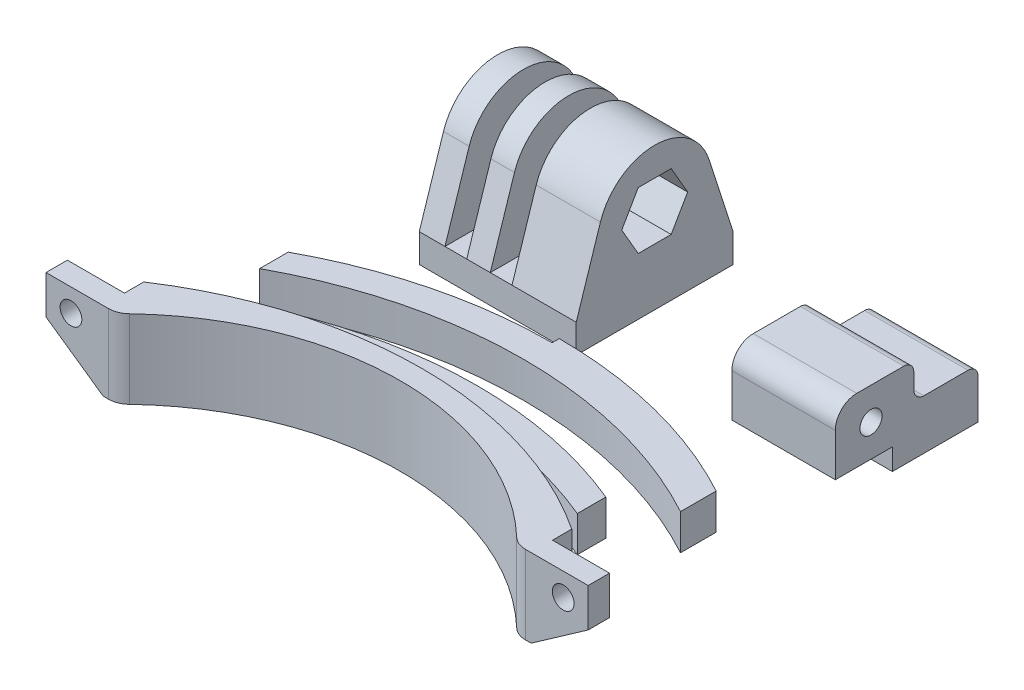
SolidWorks part; units mm, degrees
ref_plane "Front Plane" through (0, 0, 0) normal (0, 0, 1) x (1, 0, 0)
ref_plane "Top Plane" through (0, 0, 0) normal (0, 1, 0) x (1, 0, 0)
ref_plane "Right Plane" through (0, 0, 0) normal (1, 0, 0) x (0, 0, -1)
sketch "Sketch1" plane through (0, 0, 0) normal (0, 1, 0) x (1, 0, 0)
  line L0 (0, -19.7941) -> (0, 19.7941) construction
  line L1 (0, 0) -> (-30, 0) construction
  line L2 (-30, -19.7941) -> (-30, 19.7941) construction
  line L3 (30, -19.7941) -> (30, 19.7941) construction
  line L4 (-30, 0) -> (-30, -2.7)
  line L5 (-30, -2.7) -> (-38, -2.7)
  line L6 (-38, -2.7) -> (-38, -5.7)
  line L7 (-38, -5.7) -> (-28, -5.7) construction
  line L8 (30, 0) -> (30, -2.7)
  line L9 (38, -5.7) -> (29.2267, -5.7)
  line L10 (38, -2.7) -> (38, -5.7)
  line L11 (30, -2.7) -> (38, -2.7)
  line L12 (-38, -5.7) -> (-29.2267, -5.7)
  arc A0 (-30, 0) -> (30, 0) centre (0, -45.5) cw
  arc A1 (-28, -5.7) -> (28, -5.7) centre (0, -33.3543) cw construction
  arc A2 (-27.1565, -4.8713) -> (27.1565, -4.8713) centre (0, -33.3543) cw
  arc A3 (-29.2267, -5.7) -> (-27.1565, -4.8713) centre (-29.2267, -2.7) ccw
  arc A4 (29.2267, -5.7) -> (27.1565, -4.8713) centre (29.2267, -2.7) cw
  point P4 (0, 0)
  point P8 (0, 0)
  point P11 (-30, 0)
  point P13 (0, 9)
  point P25 (0, 6)
  dimension "D2" = 9
  dimension "D7" = 3
  dimension "D3" = 3
  dimension "D8" = 3
  dimension "D1" = 30
  dimension "D4" = 2.7
  dimension "D5" = 8
  dimension "D6" = 3
extrude "Boss-Extrude1" add sketch "Sketch1" along normal blind 11
sketch "Sketch2" plane through (0, 0, 5.7) normal (0, 0, 1) x (1, 0, 0)
  line L1 (0, 0) -> (0, 45.817) construction
  line L4 (-38, 0) -> (-29.2267, 0) construction
  circle A0 centre (-34.5, 7.8) radius 1.525
  circle A2 centre (34.5, 7.8) radius 1.525
  dimension "D1" = 3.05
  dimension "D2" = 7.8
  dimension "D3" = 34.5
extrude "Cut-Extrude1" cut sketch "Sketch2" against normal up to next
sketch "Sketch20" plane through (0, 0, 5.7) normal (0, 0, 1) x (1, 0, 0)
  line L0 (0, 0) -> (0, 24.4868) construction
  line L33 (-38, 0) -> (-29.2267, 0) construction
  line L38 (-38, 5.6) -> (-30, 0)
  line L39 (-38, 5.6) -> (-38, 0)
  line L40 (-38, 0) -> (-30, 0)
  line L41 (38, 0) -> (30, 0)
  line L42 (38, 5.6) -> (38, 0)
  line L43 (38, 5.6) -> (30, 0)
  dimension "D1" = 5.6
extrude "Cut-Extrude12" cut sketch "Sketch20" against normal up to next
sketch "Sketch3" plane through (0, 0, 0) normal (0, 1, 0) x (1, 0, 0)
  line L0 (0, 0) -> (0, 50000) construction
  line L1 (-29.5, 48.4144) -> (-29.5, 50048.4144) construction
  line L2 (29.5, 48.4144) -> (29.5, 50048.4144) construction
  line L3 (-0.6206, 4.7858) -> (49999.3794, 4.7858) construction
  line L4 (-29.5, 8.7858) -> (-29.5, 4.7858)
  line L5 (29.5, 8.7858) -> (29.5, 4.7858)
  arc A0 (-29.5, 4.7858) -> (29.5, 4.7858) centre (0, -45.6048) cw
  arc A1 (-29.5, 8.7858) -> (29.5, 8.7858) centre (0, -41.6048) cw
  point P14 (0, 12.7858)
  dimension "D2" = 8
  dimension "D1" = 29.5
  dimension "D3" = 2
extrude "Boss-Extrude2" add sketch "Sketch3" along normal blind 5 separate body
sketch "Sketch21" plane through (0, 5, 0) normal (0, 1, 0) x (1, 0, 0)
  line L0 (-22.5, 0.5717) -> (-22.5, 20.6377)
  line L1 (-22.5, 20.6377) -> (22.5, 20.6377)
  line L2 (22.5, 20.6377) -> (22.5, 0)
  line L3 (22.5, 0) -> (-22.5, 0.5717)
  arc A0 (29.5, 8.7858) -> (-29.5, 8.7858) centre (0, -41.6048) ccw construction
  point P7 (0, 16.7858)
  point P8 (0, 20.6377)
  arc M5 (-29.5, 4.7858) -> (29.5, 4.7858) centre (0, -45.6048) cw
  line M6 (29.5, 4.7858) -> (29.5, 8.7858)
  arc M7 (29.5, 8.7858) -> (-29.5, 8.7858) centre (0, -41.6048) ccw
  line M8 (-29.5, 8.7858) -> (-29.5, 4.7858)
  dimension "D1" = 45
extrude "Cut-Extrude11" cut sketch "Sketch21" against normal up to next (5 mm away) contours L0 M5 M7 M8 | L2 M7 M5 M6
sketch "Sketch4" plane through (0, 0, 0) normal (0, 1, 0) x (1, 0, 0)
  line L0 (0, 0) -> (0, 50000) construction
  line L1 (-29.5, -8.2678) -> (-29.5, 49991.7322) construction
  line L2 (29.5, -8.2678) -> (29.5, 49991.7322) construction
  line L3 (-0.8206, 15.7446) -> (49999.1794, 15.7446) construction
  line L4 (0, 28.2446) -> (0, 27.2446)
  line L5 (-29.5, 19.7446) -> (-29.5, 15.7446)
  line L6 (29.5, 15.7446) -> (29.5, 20.7446)
  arc A0 (-29.5, 15.7446) -> (29.5, 15.7446) centre (0, -38.522) cw
  arc A4 (-29.5, 19.7446) -> (0, 27.2446) centre (0, -34.522) cw
  arc A5 (0, 28.2446) -> (29.5, 20.7446) centre (0, -33.522) cw
  arc A6 (-22.8296, 19.8707) -> (0, 24.2446) centre (0, -37.522) cw [skipped]
  arc A7 (-22.8296, 20.8707) -> (0, 25.2446) centre (0, -36.522) cw [skipped]
  arc A8 (-22.8296, 21.8707) -> (0, 26.2446) centre (0, -35.522) cw [skipped]
  point P14 (0, 23.2446)
  dimension "D2" = 7.5
  dimension "D3" = 6
  dimension "D1" = 29.5
extrude "Boss-Extrude3" add sketch "Sketch4" along normal blind 5 separate body
sketch "Sketch10" plane through (0, 0, 0) normal (0, 1, 0) x (1, 0, 0)
  line L1 (19.99, 52.4552) -> (34.49, 52.4552)
  line L2 (19.99, 52.4552) -> (19.99, 32.4552)
  line L3 (19.99, 32.4552) -> (34.49, 32.4552)
  line L4 (34.49, 52.4552) -> (34.49, 32.4552)
  dimension "D1" = 14.5
  dimension "D2" = 20
extrude "Boss-Extrude6" add sketch "Sketch10" along normal blind 12 separate body
sketch "Sketch11" plane through (34.49, 0, 0) normal (1, 0, 0) x (0, 0, -1)
  line L0 (52.4552, 12) -> (52.4552, 0) construction
  line L1 (32.4552, 0) -> (40.4552, 0)
  line L2 (32.4552, 0) -> (32.4552, 3)
  line L3 (32.4552, 3) -> (40.4552, 3)
  line L4 (40.4552, 0) -> (40.4552, 3)
  line L5 (32.4552, 12) -> (32.4552, 9)
  line L6 (52.4552, 12) -> (42.0552, 12)
  line L8 (51.0552, 7) -> (44.8552, 7)
  line L9 (43.4552, 10.6) -> (43.4552, 8.4)
  line L10 (32.4552, 0) -> (52.4552, 0) construction
  line L11 (32.4552, 12) -> (32.4552, 0) construction
  line L12 (44.4552, 12) -> (42.0552, 12)
  line L13 (32.4552, 12) -> (35.4552, 12)
  line L14 (32.4552, 12) -> (52.4552, 12) construction
  line L15 (52.4552, 7) -> (52.4552, 12)
  line L17 (52.4552, 7) -> (52.4552, 5.6)
  arc A0 (43.4552, 10.6) -> (42.0552, 12) centre (42.0552, 10.6) ccw
  arc A1 (44.8552, 7) -> (43.4552, 8.4) centre (44.8552, 8.4) cw
  arc A2 (51.0552, 7) -> (52.4552, 5.6) centre (51.0552, 5.6) cw
  arc A3 (32.4552, 9) -> (35.4552, 12) centre (35.4552, 9) cw
  dimension "D6" = 1.4
  dimension "D8" = 1.4
  dimension "D7" = 3
  dimension "D1" = 12
  dimension "D2" = 3
  dimension "D3" = 3
  dimension "D4" = 3
  dimension "D5" = 3
  dimension "D9" = 7
extrude "Cut-Extrude5" cut sketch "Sketch11" against normal up to surface (14.5 mm away)
sketch "Sketch12" plane through (34.49, 0, 0) normal (1, 0, 0) x (0, 0, -1)
  line L7 (32.4552, 9) -> (32.4552, 3) construction
  line L8 (35.4552, 12) -> (42.0552, 12) construction
  circle A0 centre (37.4552, 7.5) radius 1.55
  dimension "D1" = 3.1
  dimension "D2" = 5
  dimension "D3" = 4.5
extrude "Cut-Extrude6" cut sketch "Sketch12" against normal up to surface (14.5 mm away) up to face at (19.99, 6.5426, -42.5609)
sketch "Sketch13" plane through (28.7111, 0, 0) normal (0, 1, 0) x (1, 0, 0)
  line L1 (-30.5078, 32.4226) -> (-52.5078, 32.4226)
  line L2 (-30.5078, 32.4226) -> (-30.5078, 54.4226)
  line L3 (-30.5078, 54.4226) -> (-52.5078, 54.4226)
  line L4 (-52.5078, 32.4226) -> (-52.5078, 54.4226)
  dimension "D1" = 22
  dimension "D2" = 22
extrude "Boss-Extrude7" add sketch "Sketch13" along normal blind 4 separate body
sketch "Sketch14" plane through (-1.7967, 0, 0) normal (1, 0, 0) x (0, 0, -1)
  line L0 (54.4226, 4) -> (54.4226, 0) construction
  line L1 (32.4226, 4) -> (54.4226, 4)
  line L2 (32.4226, 4) -> (32.4226, 22)
  line L3 (32.4226, 22) -> (54.4226, 22)
  line L4 (54.4226, 4) -> (54.4226, 22)
  circle A0 centre (43.4226, 12) radius 2.55
  point P10 (43.4226, 4)
  dimension "D2" = 8
  dimension "D3" = 5.1
  dimension "D1" = 18
extrude "Boss-Extrude8" add sketch "Sketch14" against normal up to surface (22 mm away) up to face at (-23.7967, 2, -43.4226)
sketch "Sketch15" plane through (-1.7967, 0, 0) normal (1, 0, 0) x (0, 0, -1)
  line L1 (54.4226, 4) -> (32.4226, 4) construction
  line L3 (46.6703, 15.2842) -> (42.2022, 16.4547) construction
  line L4 (42.2022, 16.4547) -> (38.9545, 13.1705) construction
  line L5 (38.9545, 13.1705) -> (40.1749, 8.7158) construction
  line L6 (40.1749, 8.7158) -> (44.6429, 7.5453) construction
  line L7 (44.6429, 7.5453) -> (47.8906, 10.8295) construction
  line L8 (47.8906, 10.8295) -> (46.6703, 15.2842) construction
  line L9 (32.4226, 4) -> (35.8118, 14.4649)
  line L10 (54.4226, 4) -> (51.0334, 14.4649)
  line L11 (32.4226, 4) -> (32.4226, 22)
  line L12 (32.4226, 22) -> (54.4226, 22)
  line L13 (54.4226, 22) -> (54.4226, 4)
  circle A0 centre (43.4226, 12) radius 8 construction
  circle A2 centre (43.4226, 12) radius 4 construction
  arc A3 (51.0334, 14.4649) -> (35.8118, 14.4649) centre (43.4226, 12) ccw
  circle A5 centre (43.4226, 12) radius 2.55 construction
  dimension "D1" = 16
  dimension "D2" = 8
extrude "Cut-Extrude7" cut sketch "Sketch15" against normal up to surface (22 mm away) up to face at (-23.7967, 11, -43.4226)
sketch "Sketch17" plane through (28.7111, 0, 0) normal (0, -1, 0) x (1, 0, 0)
  line L0 (-48.9078, -32.4226) -> (-45.8578, -32.4226)
  line L1 (-48.9078, -32.4226) -> (-48.9078, -54.4226)
  line L2 (-48.9078, -54.4226) -> (-45.8578, -54.4226)
  line L3 (-45.8578, -32.4226) -> (-45.8578, -54.4226)
  line L4 (-42.5578, -32.4226) -> (-39.5078, -32.4226)
  line L5 (-42.5578, -32.4226) -> (-42.5578, -54.4226)
  line L6 (-42.5578, -54.4226) -> (-39.5078, -54.4226)
  line L7 (-39.5078, -32.4226) -> (-39.5078, -54.4226)
  line L8 (-30.5078, -32.4226) -> (-30.5078, -54.4226) construction
  line L9 (-52.5078, -32.4226) -> (-30.5078, -32.4226) construction
  dimension "D1" = 3.05
  dimension "D2" = 3.05
  dimension "D3" = 3.3
  dimension "D4" = 9
extrude "Cut-Extrude8" cut sketch "Sketch17" against normal up to next from vertex
sketch "Sketch16" plane through (-1.7967, 0, 0) normal (1, 0, 0) x (0, 0, -1)
  line L1 (45.732, 16) -> (41.1132, 16)
  line L2 (41.1132, 16) -> (38.8038, 12)
  line L3 (38.8038, 12) -> (41.1132, 8)
  line L4 (41.1132, 8) -> (45.732, 8)
  line L5 (45.732, 8) -> (48.0414, 12)
  line L6 (48.0414, 12) -> (45.732, 16)
  circle A0 centre (43.4226, 12) radius 4 construction
  point P1 (43.4226, 16)
  dimension "D1" = 8
extrude "Cut-Extrude9" cut sketch "Sketch16" against normal offset from surface (7 mm away) 2 up to face at (-10.7967, 10.6162, -43.4226)
